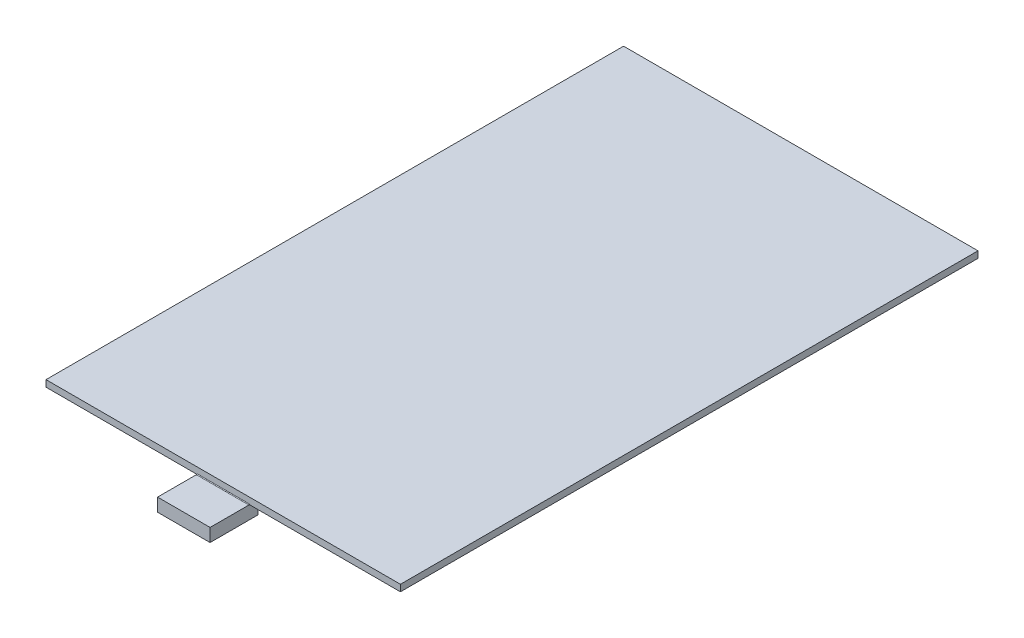
SolidWorks part; units mm, degrees
ref_plane "Front Plane" through (0, 0, 0) normal (0, 0, 1) x (1, 0, 0)
ref_plane "Top Plane" through (0, 0, 0) normal (0, 1, 0) x (1, 0, 0)
ref_plane "Right Plane" through (0, 0, 0) normal (1, 0, 0) x (0, 0, -1)
sketch "Sketch1" plane through (0, 0, 0) normal (0, 1, 0) x (1, 0, 0)
  line L1 (-27, 44) -> (27, 44)
  line L2 (-27, 44) -> (-27, -44)
  line L3 (-27, -44) -> (27, -44)
  line L4 (27, 44) -> (27, -44)
  line L5 (-27, 44) -> (27, -44) construction
  line L6 (-27, -44) -> (27, 44) construction
  point P0 (0, 0)
  dimension "D1" = 54
  dimension "D2" = 88
extrude "Boss-Extrude1" add sketch "Sketch1" along normal blind 1
sketch "Sketch2" plane through (0, 0, 0) normal (0, -1, 0) x (1, 0, 0)
  line L2 (-4, 42.7) -> (4, 42.7)
  line L3 (4, 42.7) -> (4, 44)
  line L5 (-4, 42.7) -> (-4, 44)
  line L6 (-4, 44) -> (-4, 50)
  line L7 (-4, 50) -> (4, 50)
  line L8 (4, 50) -> (4, 44)
  dimension "D2" = 1.3
  dimension "D3" = 6
extrude "Boss-Extrude2" add sketch "Sketch2" along normal blind 2
fillet "Fillet4" radius 0.1 1 edges at (0, 0, 44)
fillet "Fillet5" radius 0.1 3 edges at (4, 0, 43.35) (0, 0, 42.7) (-4, 0, 43.35)
